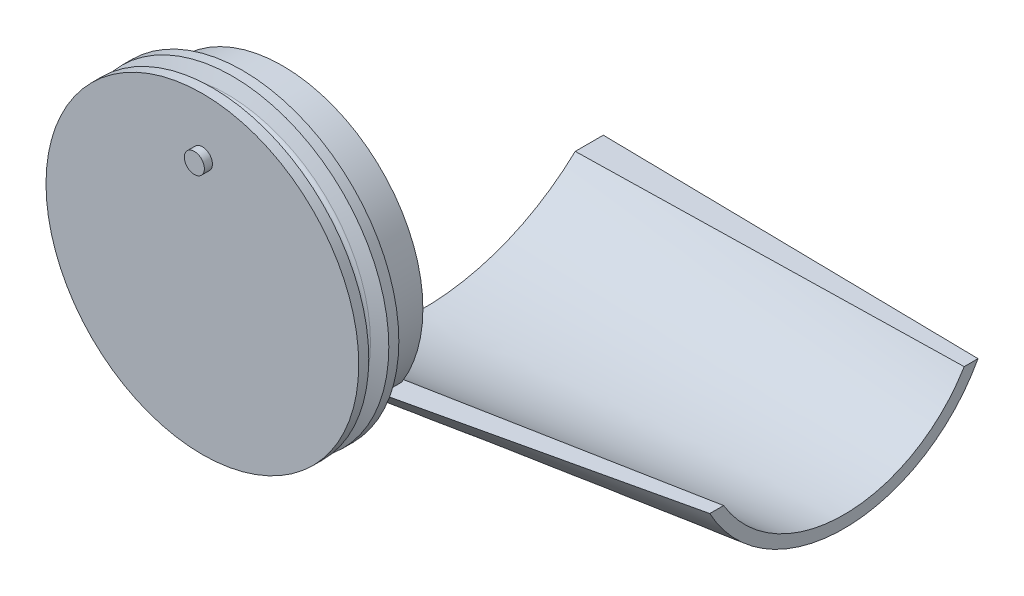
SolidWorks part; units mm, degrees
ref_plane "Front Plane" through (0, 0, 0) normal (0, 0, 1) x (1, 0, 0)
ref_plane "Top Plane" through (0, 0, 0) normal (0, 1, 0) x (1, 0, 0)
ref_plane "Right Plane" through (0, 0, 0) normal (1, 0, 0) x (0, 0, -1)
sketch "Sketch1" plane through (0, 0, 0) normal (0, 0, 1) x (1, 0, 0)
  circle A0 centre (0, 0) radius 15
  circle A1 centre (0, 0) radius 35
  dimension "D1" = 30
  dimension "D2" = 20
extrude "Boss-Extrude1" add sketch "Sketch1" along normal blind 10
sketch "Sketch2" plane through (0, 0, 0) normal (1, 0, 0) x (0, 0, -1)
  line L0 (-10, -20) -> (80, -20) construction
  line L1 (-10, -20) -> (-10, -35) construction
  line L2 (-10, -35) -> (0, -35) construction
  line L4 (35, -20) -> (35, -40) construction
  line L5 (-10, -20) -> (-2.9967, -20)
  line L6 (72.9967, -20) -> (80, -20)
  arc A0 (-10, -20) -> (80, -20) centre (35, 20.625) ccw
  arc A1 (-2.9967, -20) -> (72.9967, -20) centre (35, 20.625) ccw
  dimension "D3" = 90
  dimension "D4" = 5
  dimension "D1" = 15
  dimension "D5" = 20
ref_plane "Plane1" through (100, 0, 0) normal (1, 0, 0) x (0, 0, -1)
sketch "Sketch3" plane through (100, 0, 0) normal (1, 0, 0) x (0, 0, -1)
  line L0 (10, -15) -> (70, -15) construction
  line L1 (10, -15) -> (6.5512, -15)
  line L2 (70, -15) -> (73.4488, -15)
  line L3 (40, -15) -> (40, -35) construction
  arc A0 (10, -15) -> (70, -15) centre (40, 2.9706) ccw
  arc A4 (6.5512, -15) -> (73.4488, -15) centre (40, 2.9706) ccw
  point P2 (40, -15)
  dimension "D4" = 3
  dimension "D1" = 60
  dimension "D2" = 5
  dimension "D3" = 5
  dimension "D5" = 20
loft "Loft1" add profiles "Sketch2", "Sketch3"
sketch "Sketch5" plane through (0, 0, 10) normal (0, 0, 1) x (1, 0, 0)
  circle A0 centre (0, 0) radius 35
  dimension "D1" = 70
extrude "Boss-Extrude3" add sketch "Sketch5" along normal blind 10
ref_plane "Plane2" through (0, 0, 0) normal (-1, 0, 0) x (0, 0, 1)
sketch "Sketch7" plane through (0, 0, 0) normal (-1, 0, 0) x (0, 0, 1)
  line L0 (20, 34) -> (20, 39)
  line L1 (20, 39) -> (17.5, 39)
  line L2 (20, -35) -> (20, 35) construction
  line L3 (20, 34) -> (10, 34)
  line L4 (10, 34) -> (10, 39)
  line L5 (10, 39) -> (12.5, 39)
  line L6 (12.5, 39) -> (13.8462, 35.7692)
  line L7 (17.5, 39) -> (16.1538, 35.7692)
  line L8 (20, 35) -> (0, 35) construction
  line L9 (10, 36.25) -> (20, 36.25) construction
  arc A1 (13.8462, 35.7692) -> (16.1538, 35.7692) centre (15, 36.25) ccw
  point P16 (0, 0)
  point P17 (15, 36.25)
  point P18 (0, 0)
  point P19 (14.1021, 32.7467)
  dimension "D4" = 2.5
  dimension "D1" = 10
  dimension "D2" = 1
  dimension "D3" = 5
ref_axis "Axis1" through (0, 0, 20) along (0, 0, -1)
revolve "Revolve1" add sketch "Sketch7" angle 360 about axis through (0, 0, 20) along (0, 0, -1)
sketch "Sketch4" plane through (0, 0, 20) normal (0, 0, 1) x (1, 0, 0)
  line L0 (0, 0) -> (0, 25) construction
  circle A0 centre (0, 25) radius 2.5
  dimension "D1" = 25
  dimension "D2" = 5
extrude "Boss-Extrude2" add sketch "Sketch4" along normal blind 2
